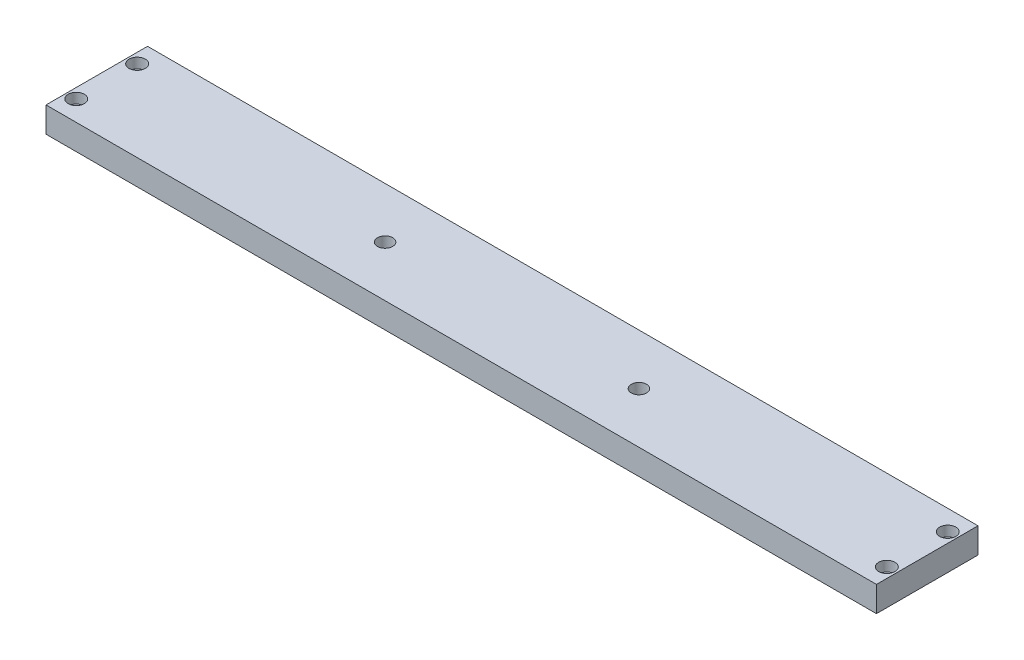
SolidWorks part; units mm, degrees
ref_plane "Front Plane" through (0, 0, 0) normal (0, 0, 1) x (1, 0, 0)
ref_plane "Top Plane" through (0, 0, 0) normal (0, 1, 0) x (1, 0, 0)
ref_plane "Right Plane" through (0, 0, 0) normal (1, 0, 0) x (0, 0, -1)
sketch "Sketch1" plane through (0, 0, 0) normal (0, 1, 0) x (1, 0, 0)
  line L1 (-81.785, -10) -> (81.785, -10)
  line L2 (-81.785, -10) -> (-81.785, 10)
  line L3 (-81.785, 10) -> (81.785, 10)
  line L4 (81.785, -10) -> (81.785, 10)
  line L5 (-81.785, -10) -> (81.785, 10) construction
  line L6 (-81.785, 10) -> (81.785, -10) construction
  circle A0 centre (-79.825, 6) radius 1
  circle A1 centre (-79.825, -6) radius 1
  circle A2 centre (79.825, 6) radius 1
  circle A3 centre (79.825, -6) radius 1
  point P0 (0, 0)
  dimension "D3" = 12
  dimension "D6" = 12
  dimension "D1" = 20
  dimension "D2" = 163.57
  dimension "D4" = 4
  dimension "D5" = 1.96
  dimension "D7" = 4
  dimension "D8" = 1.96
extrude "Boss-Extrude1" add sketch "Sketch1" along normal blind 5
sketch "Sketch2" plane through (0, 5, 0) normal (0, 1, 0) x (1, 0, 0)
  circle A0 centre (-79.825, 6) radius 1.6
  circle A1 centre (-79.825, -6) radius 1.6
  circle A2 centre (79.825, 6) radius 1.6
  circle A3 centre (79.825, -6) radius 1.6
extrude "Cut-Extrude1" cut sketch "Sketch2" against normal blind 2
sketch "Sketch3" plane through (0, 5, 0) normal (0, 1, 0) x (1, 0, 0)
  line L0 (-81.785, 10) -> (-81.785, -10) construction
  line L4 (-81.785, -10) -> (81.785, -10) construction
  circle A0 centre (-25, 0) radius 1.5
  circle A1 centre (25, 0) radius 1.5
  dimension "D1" = 50
  dimension "D2" = 56.785
  dimension "D3" = 10
  dimension "D4" = 10
extrude "Cut-Extrude2" cut sketch "Sketch3" against normal blind 10
